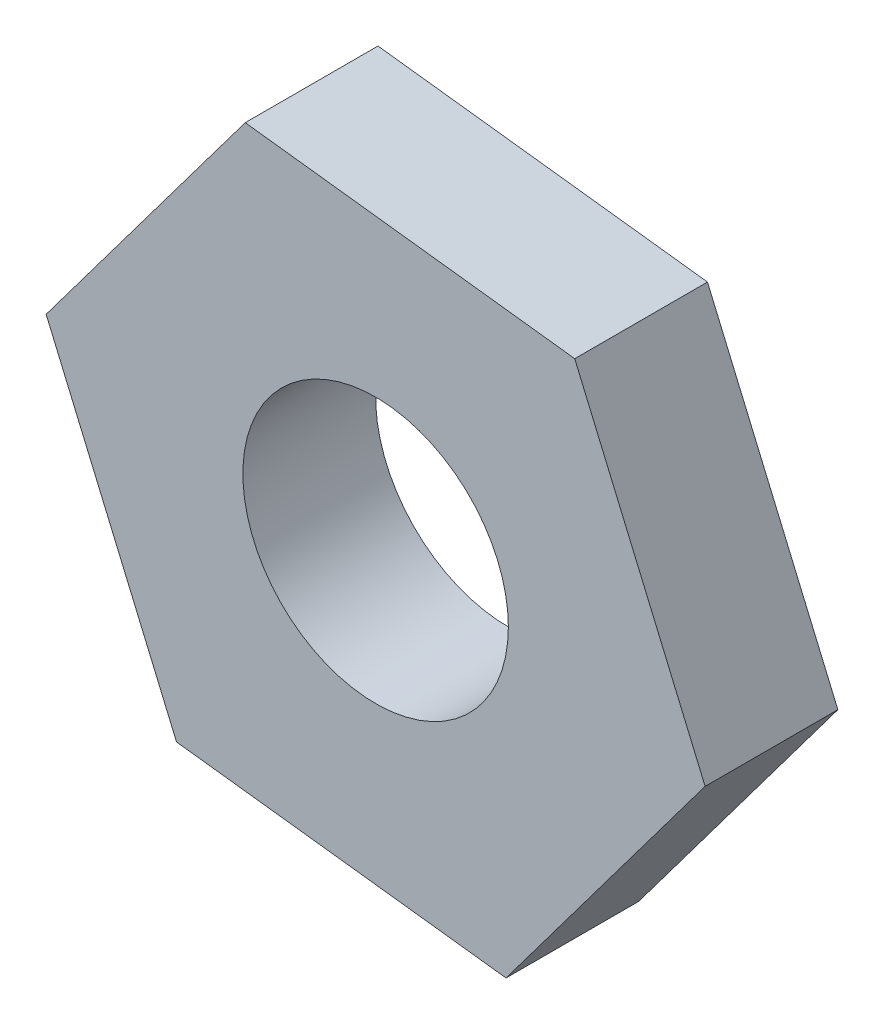
SolidWorks part; units mm, degrees
ref_plane "Front Plane" through (0, 0, 0) normal (0, 0, 1) x (1, 0, 0)
ref_plane "Top Plane" through (0, 0, 0) normal (0, 1, 0) x (1, 0, 0)
ref_plane "Right Plane" through (0, 0, 0) normal (1, 0, 0) x (0, 0, -1)
sketch "Sketch1" plane through (0, 0, 0) normal (0, 0, 1) x (1, 0, 0)
  line L1 (2.7303, 2.3022) -> (-1.1987, 11.498)
  line L2 (-1.1987, 11.498) -> (-11.127, 12.6933)
  line L3 (-11.127, 12.6933) -> (-17.1263, 4.6928)
  line L4 (-17.1263, 4.6928) -> (-13.1973, -4.503)
  line L5 (-13.1973, -4.503) -> (-3.269, -5.6983)
  line L6 (-3.269, -5.6983) -> (2.7303, 2.3022)
  circle A0 centre (-7.198, 3.4975) radius 8.6603 construction
  dimension "D1" = 10
  dimension "D2" = 10
  dimension "D3" = 10
  dimension "D4" = 10
extrude "Boss-Extrude1" add sketch "Sketch1" along normal blind 4
sketch "Sketch2" plane through (0, 0, 4) normal (0, 0, 1) x (1, 0, 0)
  circle A0 centre (-7.198, 3.4975) radius 4
  dimension "D1" = 8
extrude "Cut-Extrude1" cut sketch "Sketch2" against normal blind 4
